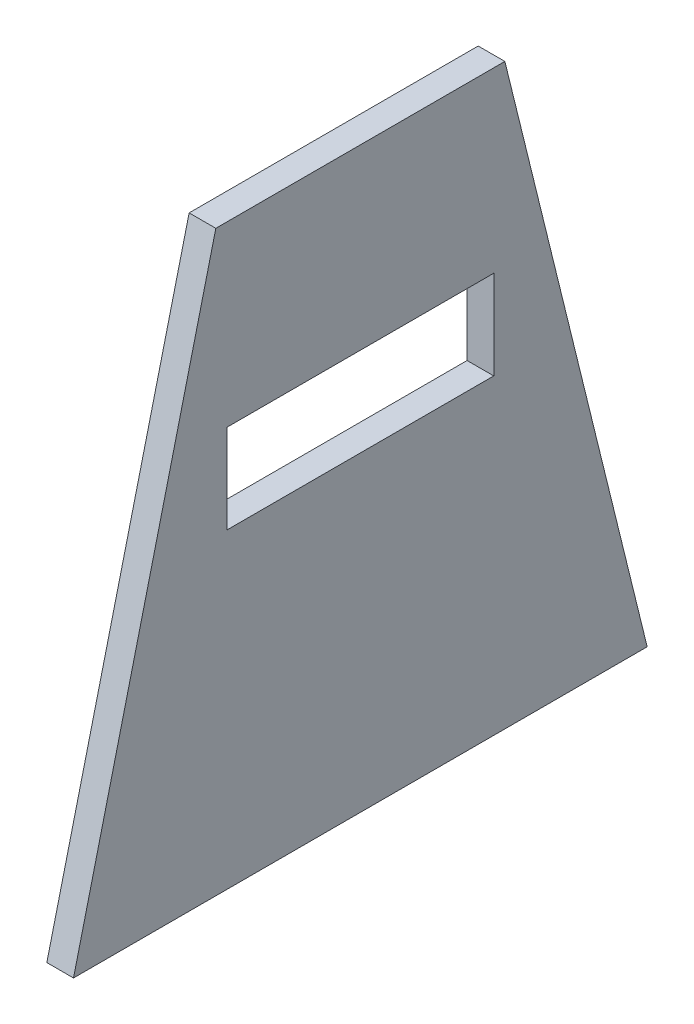
SolidWorks part; units mm, degrees
ref_plane "Alzado" through (0, 0, 0) normal (0, 0, 1) x (1, 0, 0)
ref_plane "Planta" through (0, 0, 0) normal (0, 1, 0) x (1, 0, 0)
ref_plane "Vista lateral" through (0, 0, 0) normal (1, 0, 0) x (0, 0, -1)
sketch "Croquis2" plane through (0, 0, 0) normal (1, 0, 0) x (0, 0, -1)
  line L0 (-16.25, 20) -> (16.25, 20)
  line L1 (16.25, 20) -> (32.25, -45)
  line L2 (32.25, -45) -> (-32.25, -45)
  line L3 (-32.25, -45) -> (-16.25, 20)
  line L4 (0, 0) -> (0, 34.9766) construction
  point P7 (13.75, 20.3672)
  dimension "D1" = 32.5
  dimension "D2" = 64.5
  dimension "D3" = 65
  dimension "D4" = 20
extrude "Saliente-Extruir1" add sketch "Croquis2" along normal blind 3 contours L3 L0 L1 L2
sketch "Croquis3" plane through (3, 0, 0) normal (1, 0, 0) x (0, 0, -1)
  line L0 (0, 0) -> (0, -49.3051) construction
  line L1 (15, -10) -> (-15, -10)
  line L2 (15, -10) -> (15, 0)
  line L3 (15, 0) -> (-15, 0)
  line L4 (-15, -10) -> (-15, 0)
  line L5 (15, -10) -> (-15, 0) construction
  line L6 (15, 0) -> (-15, -10) construction
  line L8 (-16.25, 20) -> (16.25, 20) construction
  point P0 (0, -5)
  dimension "D1" = 10
  dimension "D2" = 30
  dimension "D3" = 20
extrude "Cortar-Extruir1" cut sketch "Croquis3" against normal through all
